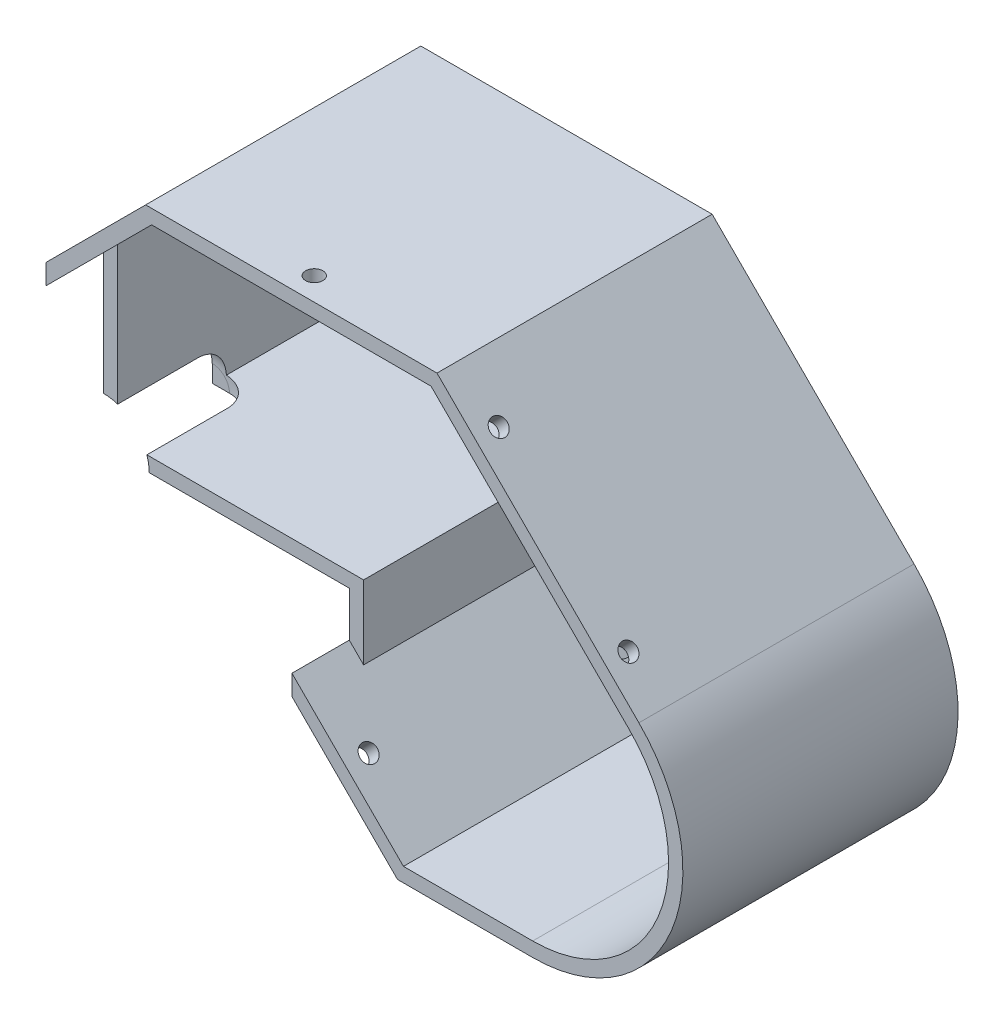
SolidWorks part; units mm, degrees
ref_plane "Plano frontal" through (0, 0, 0) normal (0, 0, 1) x (1, 0, 0)
ref_plane "Plano superior" through (0, 0, 0) normal (0, 1, 0) x (1, 0, 0)
ref_plane "Plano direito" through (0, 0, 0) normal (1, 0, 0) x (0, 0, -1)
sketch "Model" plane through (0, 0, 0) normal (0, 0, 1) x (1, 0, 0)
  line L0 (0, 0) -> (39, 0) construction
  line L1 (-0.7, 2.5) -> (39, 2.5)
  line L2 (39.7, 0) -> (39.7, -6.8548) construction
  line L3 (0, 0) -> (0, 31.4419) construction
  line L4 (50.1111, 46.949) -> (15.5071, 46.949) construction
  line L5 (0, 31.4419) -> (15.5071, 46.949) construction
  line L6 (42.2, -9.3548) -> (52.4452, -19.6) construction
  line L7 (39, -7.1448) -> (51.9502, -20.095) construction
  line L8 (97.9635, 12.6635) -> (63.6779, 46.949) construction
  line L9 (50.1111, 46.949) -> (63.6779, 46.949) construction
  line L10 (52.4452, -19.6) -> (59.4452, -26.6) construction
  line L11 (81.7, -26.6) -> (59.4452, -26.6) construction
  line L12 (-0.7, 0) -> (39, 0)
  line L13 (-0.7, 0) -> (-3.2, 0)
  line L14 (42.2, -10.3448) -> (51.9502, -20.095)
  line L15 (51.9502, -20.095) -> (59.1552, -27.3)
  line L16 (81.7, -27.3) -> (59.1552, -27.3)
  line L17 (98.4584, 13.1584) -> (63.9678, 47.649)
  line L18 (50.1111, 47.649) -> (63.9678, 47.649)
  line L19 (50.1111, 47.649) -> (15.2171, 47.649)
  line L20 (-0.7, 31.7319) -> (15.2171, 47.649)
  line L21 (-0.7, 2.5) -> (-0.7, 31.7319)
  line L22 (0, 0) -> (-0.7, 0) construction
  line L23 (38.8515, -10.5318) -> (50.1824, -21.8627) construction
  line L24 (-3.2, 0) -> (-3.2, 5)
  line L25 (-0.7, -0.7) -> (-0.7, 31.7319) construction
  line L26 (-0.7, -0.7) -> (39, -0.7) construction
  line L27 (39, -0.7) -> (39, -7.1448) construction
  line L28 (39, -0.7) -> (39, -0.7) construction
  line L29 (39, 0) -> (39.7, 0)
  line L30 (39.7, 0) -> (39.7, -11.3803)
  line L31 (39, 2.5) -> (39.7, 2.5)
  line L32 (39.7, 2.5) -> (42.2, 2.5)
  line L33 (39, 0) -> (39.7, 0) construction
  line L34 (42.2, 2.5) -> (42.2, -10.3448)
  line L35 (-3.2, 5) -> (-3.2, 32.7674)
  line L36 (-3.2, 32.7674) -> (14.1816, 50.149)
  line L37 (50.1111, 50.149) -> (14.1816, 50.149)
  line L38 (50.1111, 50.149) -> (65.0034, 50.149)
  line L39 (100.2262, 14.9262) -> (65.0034, 50.149)
  line L40 (81.7, -29.8) -> (58.1197, -29.8)
  line L41 (50.1824, -21.8627) -> (58.1197, -29.8)
  line L42 (39.7, -11.3803) -> (50.1824, -21.8627)
  line L43 (-0.7, 2.5) -> (-5.7, 2.5) construction
  line L44 (-5.7, 0) -> (-5.7, 2.5) construction
  line L45 (-0.7, 0) -> (-5.7, 0) construction
  line L46 (-3.2, 5) -> (-8.2, 5) construction
  line L47 (-8.2, -2.5) -> (-8.2, 5) construction
  line L48 (-0.7, -2.5) -> (39, -2.5) construction
  line L49 (-0.7, -2.5) -> (-8.2, -2.5) construction
  line L51 (40.6192, -8.764) -> (51.9502, -20.095) construction
  line L52 (39.7, -6.8548) -> (52.4452, -19.6) construction
  arc A0 (81.7, -27.3) -> (98.4584, 13.1584) centre (81.7, -3.6) ccw
  arc A1 (81.7, -29.8) -> (100.2262, 14.9262) centre (81.7, -3.6) ccw
  circle A2 centre (59.0726, 19.0274) radius 7.35 construction
  arc A5 (81.7, -26.6) -> (97.9635, 12.6635) centre (81.7, -3.6) ccw construction
  circle A6 centre (81.7, -3.6) radius 7.3 construction
  circle A13 centre (27.384, 23.481) radius 7.35 construction
  dimension "D2" = 2.5
  dimension "D1" = 0.7
extrude "Ressalto-extrusão1" add sketch "Model" along normal blind 48
sketch "Esboço12" plane through (57.5762, 57.5762, 0) normal (0.7071, 0.7071, 0) x (0, 0, -1)
  line L0 (-48, -35.4099) -> (-44, -35.4099) construction
  line L1 (-48, -60.3162) -> (-48, -10.5036) construction
  line L2 (-44, -35.4099) -> (-44, -43.4099) construction
  line L7 (-45.4, -52.0727) -> (-44, -52.0727) construction
  line L9 (-45.4, -20.0727) -> (-44, -20.0727) construction
  circle A0 centre (-44, -20.0727) radius 1.5
  circle A1 centre (-44, -52.0727) radius 1.5
extrude "Corte-extrusão10" cut sketch "Esboço12" against normal blind 10
sketch "Esboço13" plane through (0, 50.149, 0) normal (0, 1, 0) x (1, 0, 0)
  line L0 (39.5925, -48) -> (39.5925, -44) construction
  line L1 (65.0034, -48) -> (14.1816, -48) construction
  circle A0 centre (39.5925, -44) radius 1.5
extrude "Corte-extrusão11" cut sketch "Esboço13" against normal blind 10
sketch "Esboço14" plane through (-3.2, 0, 0) normal (-1, 0, 0) x (0, 0, 1)
  line L0 (48, 16.3837) -> (44, 16.3837) construction
  line L1 (48, 32.7674) -> (48, 0) construction
  line L2 (45.3801, 22.301) -> (45.3801, 25.101) construction
  line L3 (45.3626, 6.3583) -> (45.3626, 9.1235) construction
  line L4 (45.3801, 22.301) -> (45.3801, 25.101) construction
  line L5 (45.3626, 6.3583) -> (45.3626, 9.1235) construction
  line L6 (45.3801, 23.701) -> (44, 23.701) construction
  line L7 (45.3626, 7.7409) -> (44, 7.7409) construction
  circle A0 centre (44, 23.701) radius 1.5
  circle A1 centre (44, 7.7409) radius 1.5
extrude "Corte-extrusão12" cut sketch "Esboço14" against normal blind 10
sketch "Esboço15" plane through (14.1598, 14.1598, 0) normal (-0.7071, -0.7071, 0) x (0, 0, 1)
  line L0 (48, -62.1686) -> (44, -62.1686) construction
  line L1 (48, -62.1686) -> (0, -62.1686) construction
  line L2 (0, -36.4548) -> (0, -50.9436) construction
  line L3 (0, -50.9436) -> (0, -60.8431) construction
  line L4 (0, -36.4548) -> (0, -50.9436) construction
  line L5 (0, -50.9436) -> (0, -60.8431) construction
  line L6 (0, -60.8431) -> (0, -36.4548) construction
  line L7 (0, -36.4548) -> (0, -48.6489) construction
  line L8 (0, -48.6489) -> (48, -48.6489) construction
  line L9 (48, -36.1192) -> (48, -62.1686) construction
  line L11 (45.4, -48.2812) -> (45.4, -45.4812) construction
  line L12 (45.4, -48.2812) -> (45.4, -45.4812) construction
  line L13 (45.4, -46.8812) -> (44, -46.8812) construction
  circle A0 centre (44, -46.8812) radius 1.5
extrude "Corte-extrusão13" cut sketch "Esboço15" against normal blind 10
sketch "Esboço16" plane through (0, 0, 48) normal (0, 0, 1) x (1, 0, 0)
  line L0 (39.7, 0) -> (39.7, -7.8448)
  line L3 (42.2, -10.3448) -> (39.7, -7.8448)
  line L4 (42.2, -10.3448) -> (42.2, 2.5)
  line L5 (42.2, 2.5) -> (-0.7, 2.5)
  line L6 (39.7, 0) -> (39.7, -7.8448) construction
  line L12 (-0.7, 0) -> (39.7, 0)
  line L13 (-0.7, 2.5) -> (-0.7, 0)
extrude "Corte-extrusão14" cut sketch "Esboço16" against normal blind 10
sketch "Esboço17" plane through (0, 0, 0) normal (0, 0, -1) x (-1, 0, 0)
  line L0 (-93.3365, 21.8159) -> (-95.4578, 19.6946) construction
  line L1 (-93.3365, 21.8159) -> (-95.4578, 19.6946) construction
  line L2 (-70.709, 44.4433) -> (-72.8304, 42.322) construction
  line L3 (-70.709, 44.4433) -> (-72.8304, 42.322) construction
  line L4 (-38.0925, 50.149) -> (-41.0925, 50.149) construction
  line L5 (-38.0925, 50.149) -> (-41.0925, 50.149) construction
  line L6 (3.2, 22.201) -> (3.2, 25.201) construction
  line L7 (3.2, 22.201) -> (3.2, 25.201) construction
  line L8 (3.2, 6.2409) -> (3.2, 9.2409) construction
  line L9 (3.2, 6.2409) -> (3.2, 9.2409) construction
  line L10 (-48.3705, -20.0508) -> (-46.2492, -17.9295) construction
  line L11 (-48.3705, -20.0508) -> (-46.2492, -17.9295) construction
  line L12 (-94.3971, 20.7553) -> (-91.5687, 17.9268) construction
  line L14 (-39.5925, 50.149) -> (-39.5925, 46.149) construction
  line L18 (-69.8727, 39.6229) -> (-67.0727, 39.6229)
  line L19 (-92.9687, 19.3268) -> (-90.1687, 19.3268)
  line L20 (-92.9687, 19.3268) -> (-92.9687, 16.5268)
  line L21 (-92.9687, 16.5268) -> (-90.1687, 16.5268)
  line L22 (-90.1687, 19.3268) -> (-90.1687, 16.5268)
  line L23 (-92.9687, 19.3268) -> (-90.1687, 16.5268) construction
  line L24 (-92.9687, 16.5268) -> (-90.1687, 19.3268) construction
  line L25 (-69.8727, 39.6229) -> (-67.0727, 42.4229) construction
  line L26 (-69.8727, 42.4229) -> (-67.0727, 39.6229) construction
  line L27 (-69.8727, 42.4229) -> (-69.8727, 39.6229)
  line L28 (-69.8727, 42.4229) -> (-67.0727, 42.4229)
  line L29 (-67.0727, 42.4229) -> (-67.0727, 39.6229)
  line L30 (-38.1925, 47.549) -> (-38.1925, 44.749)
  line L31 (-40.9925, 44.749) -> (-38.1925, 47.549) construction
  line L32 (-40.9925, 47.549) -> (-40.9925, 44.749)
  line L33 (-40.9925, 47.549) -> (-38.1925, 44.749) construction
  line L34 (-40.9925, 44.749) -> (-38.1925, 44.749)
  line L35 (-40.9925, 47.549) -> (-38.1925, 47.549)
  line L36 (-2.2, 25.7837) -> (0.6, 22.9837) construction
  line L37 (-2.2, 22.9837) -> (0.6, 22.9837)
  line L38 (0.6, 25.7837) -> (0.6, 22.9837)
  line L39 (-2.2, 25.7837) -> (0.6, 25.7837)
  line L40 (-2.2, 22.9837) -> (0.6, 25.7837) construction
  line L41 (-2.2, 25.7837) -> (-2.2, 22.9837)
  line L42 (0.6, 9.7837) -> (0.6, 6.9837)
  line L43 (-2.2, 9.7837) -> (0.6, 9.7837)
  line L44 (-2.2, 6.9837) -> (0.6, 6.9837)
  line L45 (-2.2, 9.7837) -> (0.6, 6.9837) construction
  line L46 (-2.2, 9.7837) -> (-2.2, 6.9837)
  line L47 (-2.2, 6.9837) -> (0.6, 9.7837) construction
  line L48 (-52.7883, -18.8117) -> (-49.9883, -18.8117)
  line L49 (-52.7883, -16.0117) -> (-49.9883, -18.8117) construction
  line L50 (-52.7883, -18.8117) -> (-49.9883, -16.0117) construction
  line L51 (-52.7883, -16.0117) -> (-49.9883, -16.0117)
  line L52 (-49.9883, -16.0117) -> (-49.9883, -18.8117)
  line L53 (-52.7883, -16.0117) -> (-52.7883, -18.8117)
  circle A0 centre (-91.5687, 17.9268) radius 4
  circle A1 centre (-68.4727, 41.0229) radius 4
  circle A2 centre (-39.5925, 46.149) radius 4
  circle A3 centre (-0.8, 24.3837) radius 4
  circle A4 centre (-0.8, 8.3837) radius 4
  circle A5 centre (-51.3883, -17.4117) radius 4
extrude "Ressalto-extrusão2" add sketch "Esboço17" against normal blind 4
sketch "Esboço18" plane through (0, 0, 48) normal (0, 0, 1) x (1, 0, 0)
  line L0 (-0.7, 31.7319) -> (-32.4319, 0)
  line L1 (15.2171, 47.649) -> (-0.7, 31.7319) construction
  line L2 (-0.7, 31.7319) -> (-0.7, 0)
  line L3 (-0.7, 0) -> (-32.4319, 0)
extrude "Corte-extrusão15" cut sketch "Esboço18" against normal up to surface (10 mm away) up to face at (27.0667, -2.1983, 38)
sketch "Esboço19" plane through (-3.2, 0, 0) normal (-1, 0, 0) x (0, 0, 1)
  line L0 (48, -11.3803) -> (0, -11.3803) construction
  line L1 (48, -11.3803) -> (0, -11.3803) construction
  line L2 (24, -11.3803) -> (24, 0) construction
  line L3 (38, 0) -> (0, 0) construction
  line L4 (19, 0) -> (29, 0)
  line L5 (19, 0) -> (19, 3)
  line L7 (19, 3) -> (29, 3) construction
  line L8 (24, 8) -> (38.2569, 8)
  line L9 (38.2569, 8) -> (38.2569, 0)
  line L10 (38.2569, 0) -> (29, 0)
  arc A0 (24, 8) -> (19, 3) centre (24, 3) ccw
revolve "Corte-Revolução1" cut sketch "Esboço19" angle 360 about L4
